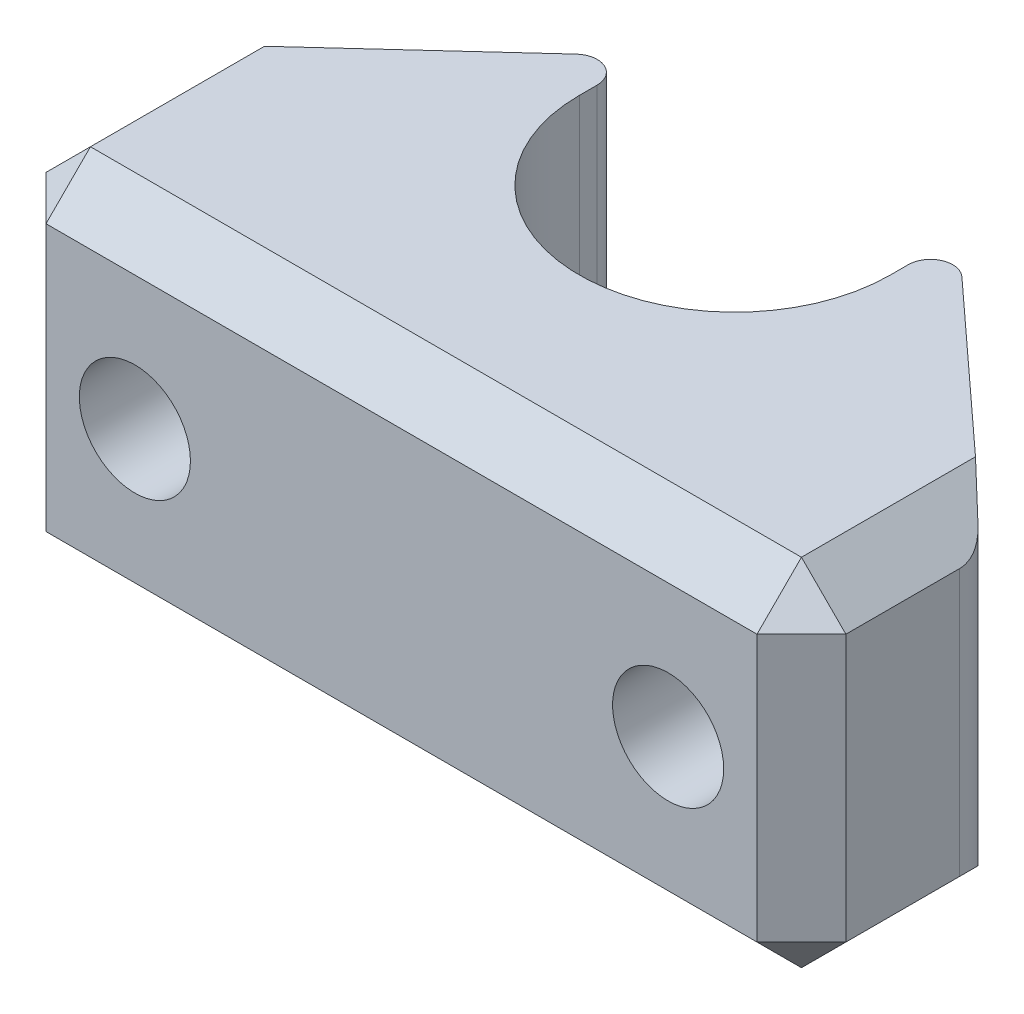
SolidWorks part; units mm, degrees
material "6061 合金"
ref_plane "前视基准面" through (0, 0, 0) normal (0, 0, 1) x (1, 0, 0)
ref_plane "上视基准面" through (0, 0, 0) normal (0, 1, 0) x (1, 0, 0)
ref_plane "右视基准面" through (0, 0, 0) normal (1, 0, 0) x (0, 0, -1)
sketch "草图1" plane through (0, 0, 0) normal (0, 1, 0) x (1, 0, 0)
  line L0 (9, -7.5) -> (-9, -7.5)
  line L1 (-9, -7.5) -> (-9, -3.5)
  line L2 (-9, -3.5) -> (-2.3646, 2.5804)
  line L3 (0, -4.4) -> (0, 4.4) construction
  line L4 (9, -3.5) -> (2.3646, 2.5804)
  line L5 (9, -7.5) -> (9, -3.5)
  circle A0 centre (0, 0) radius 2
  arc A1 (-2.3646, 2.5804) -> (2.3646, 2.5804) centre (0, 0) cw
  dimension "D1" = 4
  dimension "D2" = 3.5
  dimension "D3" = 7.5
  dimension "D4" = 18
  dimension "D5" = 4
extrude "凸台-拉伸1" add sketch "草图1" along normal mid plane 8
hole_wizard "M3 螺纹孔1" positions "草图2" profile "草图3" tap size "M3" standard "GB" end condition through all
sketch "草图2" plane through (0, 0, 7.5) normal (0, 0, 1) x (1, 0, 0)
  line L0 (-6, 0) -> (6, 0) construction
  point P0 (-6, 0)
  point P4 (6, 0)
  dimension "D1" = 12
cosmetic thread "孔螺蚊线1" parameters "D2"=3
cosmetic thread "孔螺蚊线2" parameters "D2"=3
sketch "草图3" plane through (-6, 0, 7.5) normal (1, 0, 0) x (0, -1, 0)
  line L0 (0, 0) -> (0, 11)
  line L1 (0, 11) -> (1.25, 11)
  line L2 (1.25, 11) -> (1.25, 0)
  line L5 (1.25, 0) -> (0, 0)
  line L11 (0, -6.35) -> (0, 107.95) construction
  dimension "通孔螺纹孔钻头直径" = 2.5
  dimension "通孔螺纹孔钻头深度" = 11
sketch "草图4" plane through (0, 4, 0) normal (0, 1, 0) x (1, 0, 0)
  line L0 (-3.5, 0) -> (-3.5, 1.54)
  line L1 (-2.3646, 2.5804) -> (-9, -3.5) construction
  line L2 (0, -4.4) -> (0, 4.4) construction
  line L3 (3.5, 0) -> (3.5, 1.54)
  line L4 (9, -3.5) -> (2.3646, 2.5804) construction
  line L5 (3.5, 1.54) -> (2.3646, 2.5804)
  line L6 (-2.3646, 2.5804) -> (-3.5, 1.54)
  arc A0 (-3.5, 0) -> (3.5, 0) centre (0, 0) ccw
  arc A1 (2.3646, 2.5804) -> (-2.3646, 2.5804) centre (0, 0) ccw construction
  arc A2 (2.3646, 2.5804) -> (-2.3646, 2.5804) centre (0, 0) ccw
  dimension "D1" = 7
extrude "切除-拉伸1" cut sketch "草图4" against normal blind 5
chamfer "倒角1" distance 1 angle 45 8 edges at (-9, 4, 5.5) (0, -4, 7.5) (-9, 0, 7.5) (9, 4, 5.5) (0, 4, 7.5) (9, 0, 7.5) (-9, -4, 5.5) (9, -4, 5.5)
fillet "圆角1" radius 1 2 edges at (9, 0, 3.5) (-9, 0, 3.5)
fillet "圆角2" radius 0.5 2 edges at (3.5, 1.5, -1.54) (-3.5, 1.5, -1.54)
